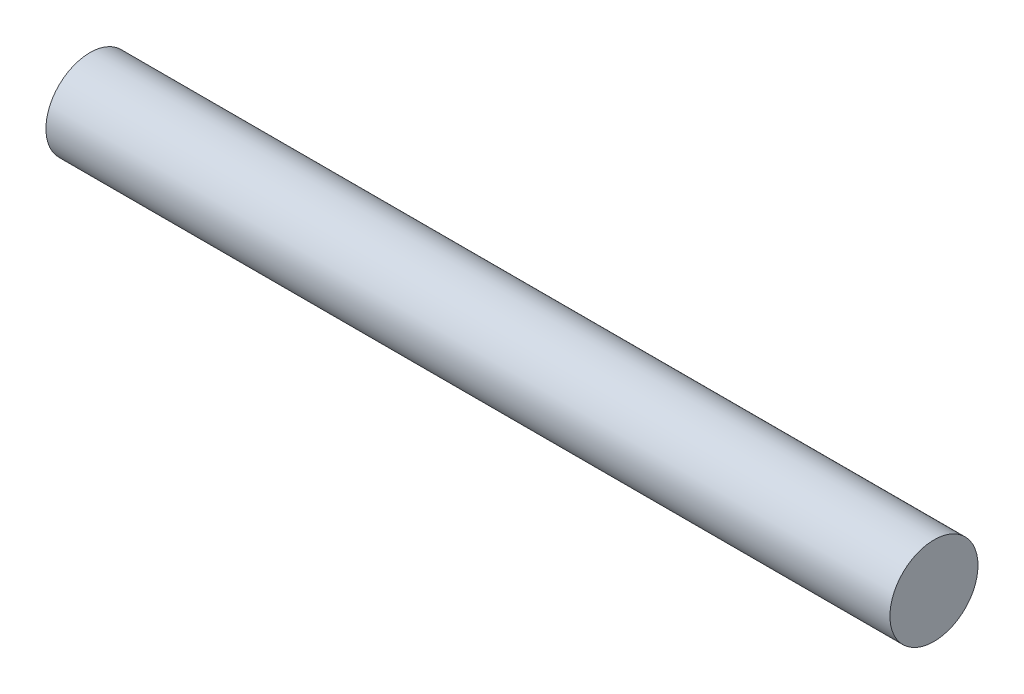
SolidWorks part; units mm, degrees
ref_plane "Front Plane" through (0, 0, 0) normal (0, 0, 1) x (1, 0, 0)
ref_plane "Top Plane" through (0, 0, 0) normal (0, 1, 0) x (1, 0, 0)
ref_plane "Right Plane" through (0, 0, 0) normal (1, 0, 0) x (0, 0, -1)
sketch "Sketch1" plane through (0, 0, 0) normal (1, 0, 0) x (0, 0, -1)
  circle A0 centre (0, 0) radius 1.2
extrude "Boss-Extrude1" add sketch "Sketch1" along normal blind 23
